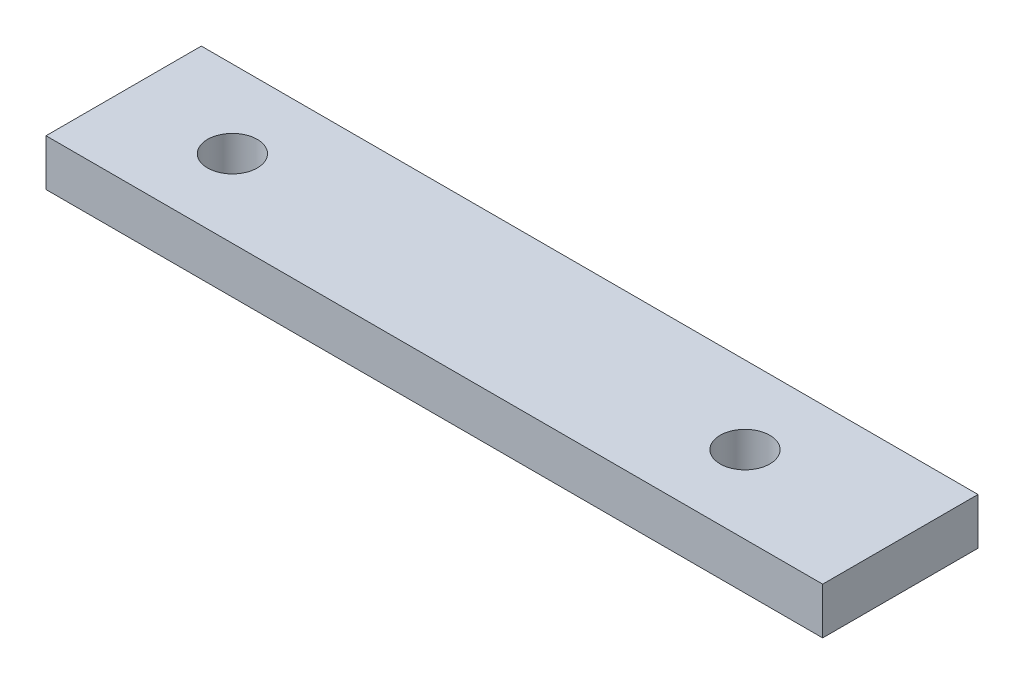
SolidWorks part; units mm, degrees
material "PBT General Purpose"
ref_plane "Front Plane" through (0, 0, 0) normal (0, 0, 1) x (1, 0, 0)
ref_plane "Top Plane" through (0, 0, 0) normal (0, 1, 0) x (1, 0, 0)
ref_plane "Right Plane" through (0, 0, 0) normal (1, 0, 0) x (0, 0, -1)
sketch "Sketch1" plane through (0, 0, 0) normal (0, 1, 0) x (1, 0, 0)
  line L0 (0, 0) -> (50, 0)
  line L1 (0, 0) -> (0, 10)
  line L2 (50, 0) -> (50, 10)
  line L3 (0, 10) -> (50, 10)
  line L4 (0, 5) -> (50, 5) construction
  circle A0 centre (7, 5) radius 1.6
  circle A1 centre (40, 5) radius 1.6
  point P15 (50, 0)
  point P18 (0, 0)
  point P21 (0, 10)
  dimension "D3" = 3.2
  dimension "D4" = 3.2
  dimension "D5" = 10
  dimension "D6" = 43
  dimension "D1" = 10
  dimension "D2" = 50
extrude "Boss-Extrude1" add sketch "Sketch1" along normal blind 3
